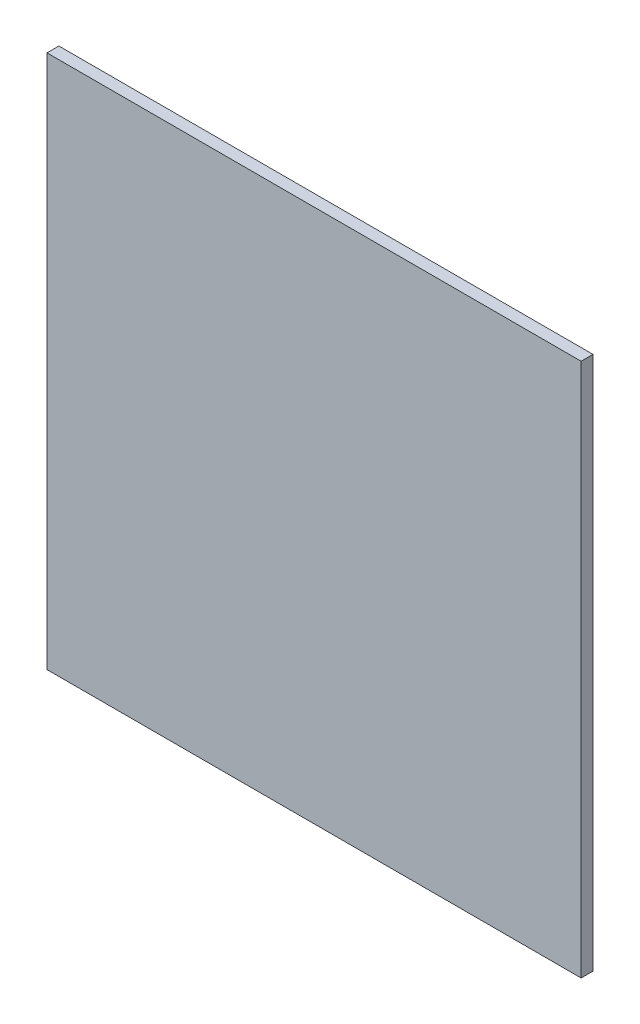
SolidWorks part; units mm, degrees
ref_plane "Front" through (0, 0, 0) normal (0, 0, 1) x (1, 0, 0)
ref_plane "Top" through (0, 0, 0) normal (0, 1, 0) x (1, 0, 0)
ref_plane "Right" through (0, 0, 0) normal (1, 0, 0) x (0, 0, -1)
sketch "Эскиз1" plane through (0, 0, 0) normal (0, 0, 1) x (1, 0, 0)
  line L1 (-22.5, -22.5) -> (22.5, -22.5)
  line L2 (-22.5, -22.5) -> (-22.5, 22.5)
  line L3 (-22.5, 22.5) -> (22.5, 22.5)
  line L4 (22.5, -22.5) -> (22.5, 22.5)
  line L5 (-22.5, -22.5) -> (22.5, 22.5) construction
  line L6 (-22.5, 22.5) -> (22.5, -22.5) construction
  point P0 (0, 0)
  dimension "D1" = 45
extrude "Бобышка-Вытянуть1" add sketch "Эскиз1" along normal blind 1
